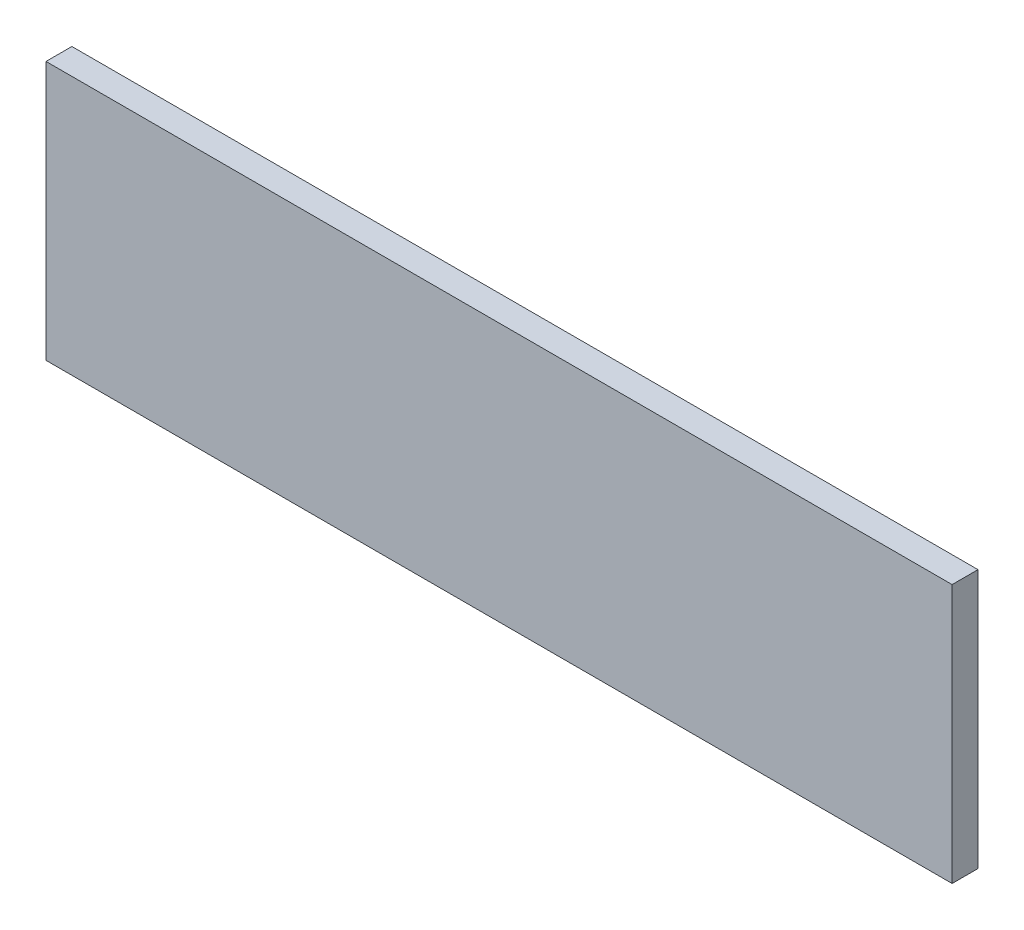
SolidWorks part; units mm, degrees
ref_plane "Спереди" through (0, 0, 0) normal (0, 0, 1) x (1, 0, 0)
ref_plane "Сверху" through (0, 0, 0) normal (0, 1, 0) x (1, 0, 0)
ref_plane "Справа" through (0, 0, 0) normal (1, 0, 0) x (0, 0, -1)
sketch "Эскиз1" plane through (0, 0, 0) normal (0, 0, 1) x (1, 0, 0)
  line L1 (0, 0) -> (70, 0)
  line L2 (0, 0) -> (0, -20)
  line L3 (0, -20) -> (70, -20)
  line L4 (70, 0) -> (70, -20)
extrude "Бобышка-Вытянуть1" add sketch "Эскиз1" along normal blind 2
